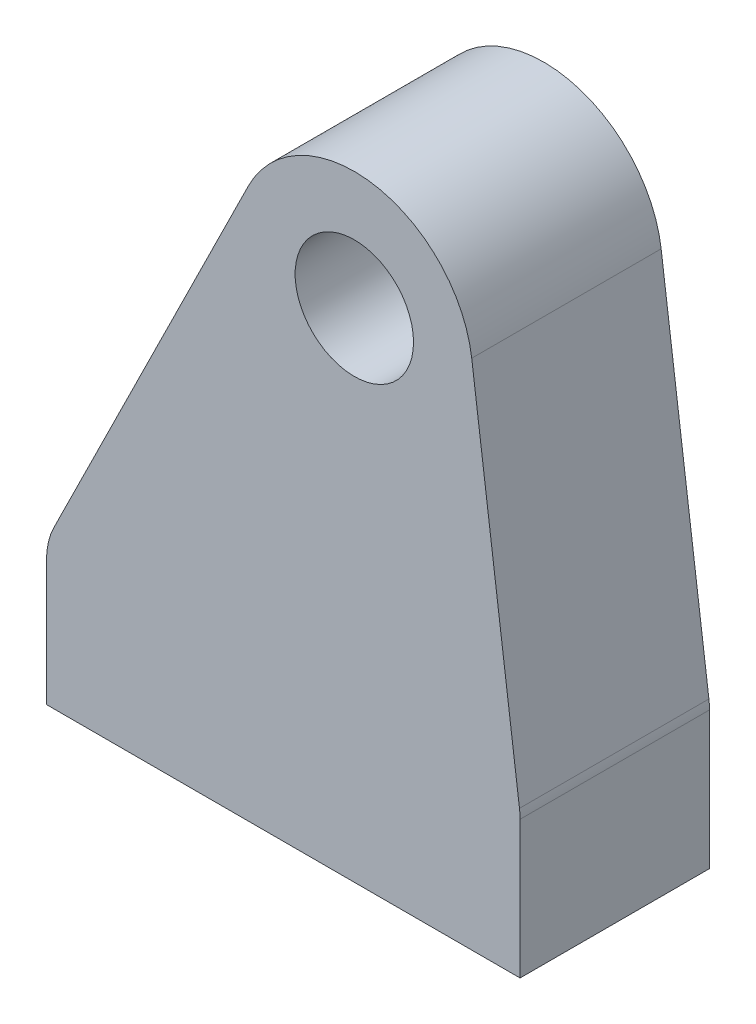
SolidWorks part; units mm, degrees
material "6061 合金"
ref_plane "前视基准面" through (0, 0, 0) normal (0, 0, 1) x (1, 0, 0)
ref_plane "上视基准面" through (0, 0, 0) normal (0, 1, 0) x (1, 0, 0)
ref_plane "右视基准面" through (0, 0, 0) normal (1, 0, 0) x (0, 0, -1)
sketch "草图1" plane through (0, 0, 0) normal (0, 0, 1) x (1, 0, 0)
  line L0 (-10, 0) -> (10, 0)
  line L1 (10, 0) -> (10, 6)
  line L4 (-10, 6) -> (-10, 0)
  line L5 (-10, 0) -> (-10, -3) construction
  line L6 (-10, -3) -> (10, -3) construction
  line L7 (10, -3) -> (10, 0) construction
  line L8 (-10, 6) -> (-1.4815, 23.2173)
  line L9 (7.958, 21.647) -> (10, 6)
  circle A3 centre (3, 21) radius 2.5
  arc A4 (7.958, 21.647) -> (-1.4815, 23.2173) centre (3, 21) ccw
  dimension "D3" = 21
  dimension "D4" = 5
  dimension "D6" = 3
  dimension "D7" = 10
  dimension "D1" = 6
  dimension "D2" = 20
  dimension "D5" = 3
extrude "凸台-拉伸1" add sketch "草图1" along normal blind 8
cosmetic thread "装饰螺纹线3" parameters "D2"=6
sketch "草图2" plane through (0, 0, 0) normal (0, -1, 0) x (1, 0, 0)
  line L0 (-10, 4) -> (-6, 4) construction
  line L1 (-10, 8) -> (-10, 0) construction
  line L2 (-6, 4) -> (6, 4) construction
  line L3 (6, 4) -> (10, 4) construction
  line L4 (10, 8) -> (10, 0) construction
  circle A0 centre (-6, 4) radius 1.5
  circle A1 centre (6, 4) radius 1.5
  dimension "D2" = 3
  dimension "D1" = 12
extrude "切除-拉伸1" cut sketch "草图2" against normal blind 10
cosmetic thread "装饰螺纹线1" parameters "D2"=4
cosmetic thread "装饰螺纹线2" parameters "D2"=4
fillet "圆角1" radius 3 2 edges at (10, 6, 4) (-10, 6, 4)
